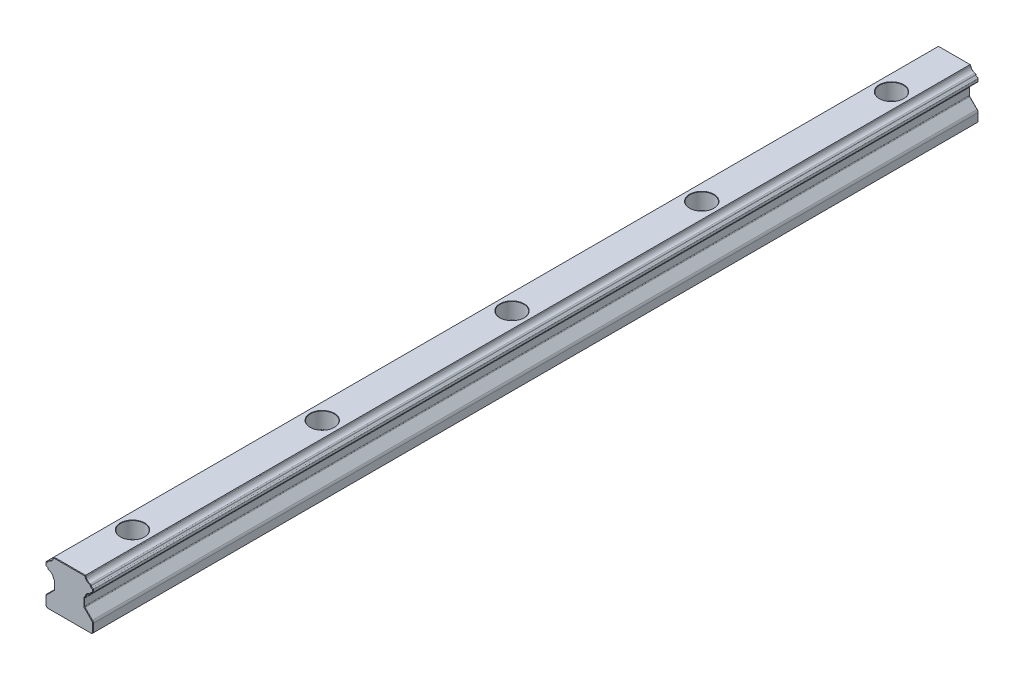
SolidWorks part; units mm, degrees
material "Plain Carbon Steel"
ref_plane "Front Plane" through (0, 0, 0) normal (0, 0, 1) x (1, 0, 0)
ref_plane "Top Plane" through (0, 0, 0) normal (0, 1, 0) x (1, 0, 0)
ref_plane "Right Plane" through (0, 0, 0) normal (1, 0, 0) x (0, 0, -1)
sketch "Rail Profile" plane through (0, 0, 0) normal (0, 0, 1) x (1, 0, 0)
  line L47 (0, 0) -> (0, 20) construction
  line L48 (-7, 0) -> (7, 0)
  line L49 (7, 0) -> (7.5, 0.5)
  line L50 (7.5, 0.5) -> (7.5, 3.0858)
  line L58 (7.2071, 3.7929) -> (4.8672, 6.1328)
  line L59 (4.75, 6.4157) -> (4.75, 8.5843)
  line L60 (4.8672, 8.8672) -> (5.063, 9.063)
  line L61 (7.5, 11.6657) -> (7.5, 12.3343)
  line L62 (-7, 0) -> (-7.5, 0.5)
  line L63 (5, 15) -> (-5, 15)
  line L64 (6.75, 9) -> (6.75, 15) construction
  line L65 (5.063, 14.937) -> (5, 15)
  line L66 (-7.5, 0.5) -> (-7.5, 3.0858)
  line L67 (6.75, 15) -> (3.75, 12) construction
  line L68 (3.75, 12) -> (6.75, 9) construction
  line L69 (7.1, 12.3343) -> (7.1, 11.6657) construction
  line L70 (6.4042, 13.0301) -> (6.4042, 10.9699) construction
  line L71 (-7.2071, 3.7929) -> (-4.8672, 6.1328)
  line L72 (-4.75, 6.4157) -> (-4.75, 8.5843)
  line L73 (-4.8672, 8.8672) -> (-5.063, 9.063)
  line L74 (5, 15) -> (8, 12) construction
  line L75 (4.8672, 8.8672) -> (8, 12) construction
  line L76 (-7.5, 11.6657) -> (-7.5, 12.3343)
  line L77 (-5.063, 14.937) -> (-5, 15)
  arc A4 (6.4734, 13.4241) -> (5.1741, 14.7234) centre (6.75, 15) cw
  arc A6 (5.1741, 9.2766) -> (6.4734, 10.5759) centre (6.75, 9) cw
  arc A7 (7.2071, 3.7929) -> (7.5, 3.0858) centre (6.5, 3.0858) cw
  arc A8 (5.063, 14.937) -> (5.1741, 14.7234) centre (4.7801, 14.6542) cw
  arc A9 (6.4734, 13.4241) -> (6.8012, 13.0792) centre (6.4042, 13.0301) cw
  arc A10 (7.1491, 12.7313) -> (7.5, 12.3343) centre (7.1, 12.3343) cw
  arc A11 (7.5, 11.6657) -> (7.1491, 11.2687) centre (7.1, 11.6657) cw
  arc A12 (6.8012, 10.9208) -> (6.4734, 10.5759) centre (6.4042, 10.9699) cw
  arc A13 (5.1741, 9.2766) -> (5.063, 9.063) centre (4.7801, 9.3458) cw
  arc A14 (4.8672, 8.8672) -> (4.75, 8.5843) centre (5.15, 8.5843) ccw
  arc A15 (4.75, 6.4157) -> (4.8672, 6.1328) centre (5.15, 6.4157) ccw
  arc A16 (6.8012, 13.0792) -> (7.1491, 12.7313) centre (7.1981, 13.1283) ccw
  arc A17 (7.1491, 11.2687) -> (6.8012, 10.9208) centre (7.1981, 10.8717) ccw
  arc A18 (-7.2071, 3.7929) -> (-7.5, 3.0858) centre (-6.5, 3.0858) ccw
  arc A19 (-4.75, 6.4157) -> (-4.8672, 6.1328) centre (-5.15, 6.4157) cw
  arc A20 (-4.8672, 8.8672) -> (-4.75, 8.5843) centre (-5.15, 8.5843) cw
  arc A21 (-5.1741, 9.2766) -> (-5.063, 9.063) centre (-4.7801, 9.3458) ccw
  arc A22 (-5.1741, 9.2766) -> (-6.4734, 10.5759) centre (-6.75, 9) ccw
  arc A23 (-6.8012, 10.9208) -> (-6.4734, 10.5759) centre (-6.4042, 10.9699) ccw
  arc A24 (-7.1491, 11.2687) -> (-6.8012, 10.9208) centre (-7.1981, 10.8717) cw
  arc A25 (-7.5, 11.6657) -> (-7.1491, 11.2687) centre (-7.1, 11.6657) ccw
  arc A26 (-7.1491, 12.7313) -> (-7.5, 12.3343) centre (-7.1, 12.3343) ccw
  arc A27 (-6.8012, 13.0792) -> (-7.1491, 12.7313) centre (-7.1981, 13.1283) cw
  arc A28 (-6.4734, 13.4241) -> (-6.8012, 13.0792) centre (-6.4042, 13.0301) ccw
  arc A29 (-6.4734, 13.4241) -> (-5.1741, 14.7234) centre (-6.75, 15) ccw
  arc A30 (-5.063, 14.937) -> (-5.1741, 14.7234) centre (-4.7801, 14.6542) ccw
  point P2 (4.75, 7.5)
  point P12 (7.5, 12)
  point P19 (6.75, 12)
  point P25 (5.1578, 14.8422)
  point P50 (8, 12)
  point P78 (0, 15)
  dimension "Rb" = 1.6
  dimension "Rf1" = 1
  dimension "Rf2" = 0.4
  dimension "WR" = 15
  dimension "Wi" = 9.5
  dimension "Wt" = 5
  dimension "Ac" = 135
  dimension "HR" = 15
  dimension "Hm" = 7.5
  dimension "Hb" = 12
  dimension "Hc" = 0.5
  dimension "Wb" = 7.5
extrude "Body" add sketch "Rail Profile" against normal blind 280
chamfer "Aesthetic Chamfer" distance 0.15 angle 45 84 edges at (-5.0315, 14.9685, 0) (-5.135, 14.8388, 0) (-5.6186, 13.8686, 0) (-6.6941, 13.3057, 0) (-6.9153, 12.8454, 0) (-7.3997, 12.5992, 0) (-7.5, 12, 0) (-7.3997, 11.4008, 0) (-6.9153, 11.1546, 0) (-6.6941, 10.6943, 0) (-5.6186, 10.1314, 0) (-5.135, 9.1612, 0) (-4.9651, 8.9651, 0) (-4.7804, 8.7374, 0) (-4.75, 7.5, 0) (-4.7804, 6.2626, 0) (-6.0371, 4.9629, 0) (-7.4239, 3.4685, 0) (-7.5, 1.7929, 0) (-7.25, 0.25, 0) (0, 0, 0) (7.25, 0.25, 0) (5.0315, 14.9685, 0) (5.135, 14.8388, 0) (5.6186, 13.8686, 0) (6.6941, 13.3057, 0) (6.9153, 12.8454, 0) (7.3997, 12.5992, 0) (7.5, 12, 0) (7.3997, 11.4008, 0) (6.9153, 11.1546, 0) (6.6941, 10.6943, 0) (5.6186, 10.1314, 0) (5.135, 9.1612, 0) (4.9651, 8.9651, 0) (4.7804, 8.7374, 0) (7.5, 1.7929, 0) (4.75, 7.5, 0) (7.4239, 3.4685, 0) (4.7804, 6.2626, 0) (6.0371, 4.9629, 0) (0, 15, 0) (5.0315, 14.9685, -280) (5.135, 14.8388, -280) (5.6186, 13.8686, -280) (6.6941, 13.3057, -280) (6.9153, 12.8454, -280) (7.3997, 12.5992, -280) (7.5, 12, -280) (7.3997, 11.4008, -280) (6.9153, 11.1546, -280) (6.6941, 10.6943, -280) (5.6186, 10.1314, -280) (5.135, 9.1612, -280) (4.9651, 8.9651, -280) (4.7804, 8.7374, -280) (4.75, 7.5, -280) (4.7804, 6.2626, -280) (6.0371, 4.9629, -280) (7.4239, 3.4685, -280) (7.5, 1.7929, -280) (7.25, 0.25, -280) (0, 0, -280) (-7.25, 0.25, -280) (-5.0315, 14.9685, -280) (-5.135, 14.8388, -280) (-5.6186, 13.8686, -280) (-6.6941, 13.3057, -280) (-6.9153, 12.8454, -280) (-7.3997, 12.5992, -280) (-7.5, 12, -280) (-7.3997, 11.4008, -280) (-6.9153, 11.1546, -280) (-6.6941, 10.6943, -280) (-5.6186, 10.1314, -280) (-7.5, 1.7929, -280) (-5.135, 9.1612, -280) (-7.4239, 3.4685, -280) (-4.9651, 8.9651, -280) (-6.0371, 4.9629, -280) (-4.7804, 8.7374, -280) (-4.7804, 6.2626, -280) (-4.75, 7.5, -280) (0, 15, -280)
hole_wizard "Mounting Hole" positions "3DSketch1" profile "Sketch1" counterbore size "M4" standard "ISO" end condition through all
sketch3d "3DSketch1"
  point P0 (0, 15, -20)
  dimension "D1" = 7.5
  dimension "E1" = 20
sketch "Sketch1" plane through (0, 15, -20) normal (1, 0, 0) x (0, 0, 1)
  line L0 (0, 0) -> (0, 15)
  line L1 (2.25, 14.9) -> (2.35, 15)
  line L2 (2.25, 14.9) -> (2.25, 5.4)
  line L3 (2.25, 5.4) -> (2.35, 5.3)
  line L4 (2.35, 5.3) -> (3.75, 5.3)
  line L5 (3.75, 5.3) -> (3.75, 0.1)
  line L6 (3.75, 0.1) -> (3.85, 0)
  line L7 (3.85, 0) -> (0, 0)
  line L8 (-3.75, 0.1) -> (-3.85, 0) construction
  line L9 (-2.25, 5.4) -> (-2.35, 5.3) construction
  line L11 (0, -6.35) -> (0, 107.95) construction
  line L12 (2.35, 15) -> (0, 15)
  line L13 (-2.25, 14.9) -> (-2.35, 15) construction
  dimension "Thru Hole Dia." = 4.5
  dimension "Thru Hole Depth" = 15
  dimension "C'Bore Dia." = 7.5
  dimension "C'Bore Depth" = 5.3
  dimension "Near C'Sink Dia." = 7.7
  dimension "Near C'Sink Angle" = 90
  dimension "Mid C'Sink Dia." = 4.7
  dimension "Mid C'Sink Angle" = 90
  dimension "Far C'Sink Dia." = 4.7
  dimension "Far C'Sink Angle" = 90
fillet "Production Fillet" radius 0.1 1 edges at (0, 9.7, -16.25)
pattern_linear "Mounting Holes Pattern" count 5 spacing 60 along (0, 0, -1) of "Mounting Hole", "Production Fillet"
equation "\"Wt@Rail Profile\"= \"WR@Rail Profile\" / 3'Top Side Half Width"
equation "\"Hm@Rail Profile\"= \"HR@Rail Profile\" / 2'Recirculation Avoidance Height"
equation "\"Hb@Rail Profile\"= 0.8 * \"HR@Rail Profile\"'Pivot Height"
equation "\"Hc@Rail Profile\"= \"WR@Rail Profile\" / 30'Chamfer Width"
equation "\"Wb@Rail Profile\"= \"WR@Rail Profile\" / 2'Ball Center Cross Width"
equation "\"D1@3DSketch1\"= \"WR@Rail Profile\" / 2'Hole Center Position"
